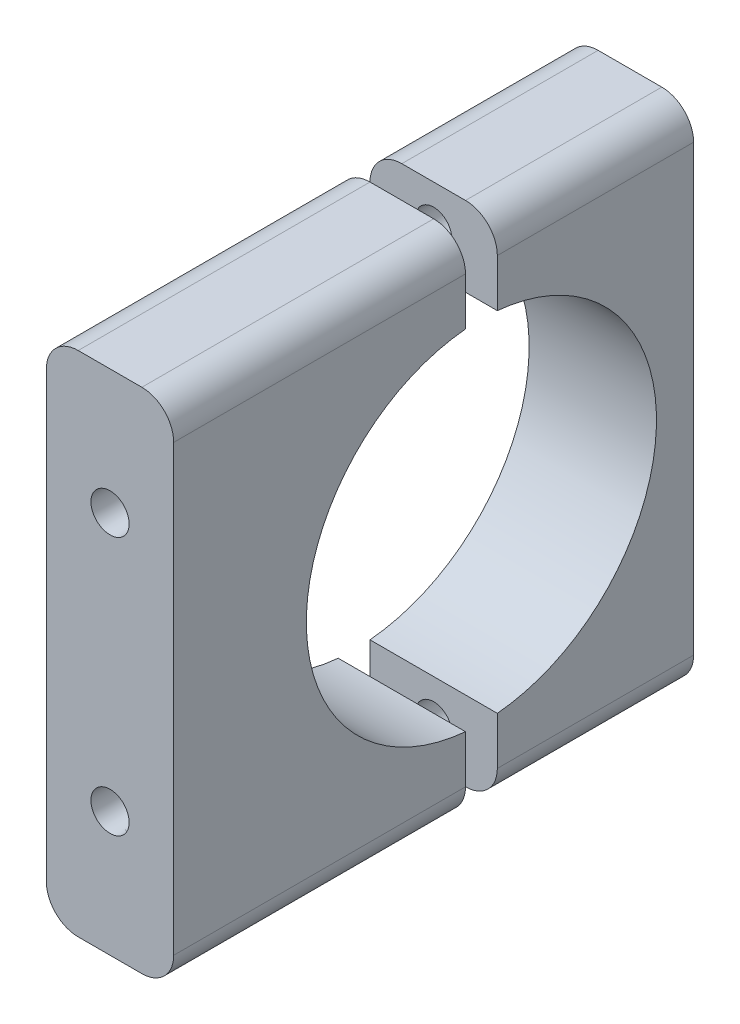
SolidWorks part; units mm, degrees
material "ABS"
ref_plane "Front Plane" through (0, 0, 0) normal (0, 0, 1) x (1, 0, 0)
ref_plane "Top Plane" through (0, 0, 0) normal (0, 1, 0) x (1, 0, 0)
ref_plane "Right Plane" through (0, 0, 0) normal (1, 0, 0) x (0, 0, -1)
sketch "Sketch1" plane through (0, 0, 0) normal (1, 0, 0) x (0, 0, -1)
  line L0 (-1.5, 16.4317) -> (-1.5, 23.9317) construction
  line L1 (-1.5, 23.9317) -> (-29, 23.9317) construction
  line L2 (-29, 23.9317) -> (-29, -23.9317) construction
  line L3 (-29, -23.9317) -> (-1.5, -23.9317) construction
  line L4 (-1.5, -23.9317) -> (-1.5, -16.4317) construction
  line L5 (1.5, 23.9317) -> (1.5, 16.4317) construction
  line L6 (20, 23.9317) -> (1.5, 23.9317) construction
  line L7 (20, -23.9317) -> (20, 23.9317) construction
  line L8 (1.5, -23.9317) -> (20, -23.9317) construction
  line L9 (1.5, -16.4317) -> (1.5, -23.9317) construction
  line L10 (-1.5, 16.4317) -> (-1.5, 23.9317)
  line L11 (-1.5, 23.9317) -> (-29, 23.9317)
  line L12 (-29, 23.9317) -> (-29, -23.9317)
  line L13 (-29, -23.9317) -> (-1.5, -23.9317)
  line L14 (-1.5, -23.9317) -> (-1.5, -16.4317)
  line L15 (1.5, 23.9317) -> (1.5, 16.4317)
  line L16 (20, 23.9317) -> (1.5, 23.9317)
  line L17 (20, -23.9317) -> (20, 23.9317)
  line L18 (1.5, -23.9317) -> (20, -23.9317)
  line L19 (1.5, -16.4317) -> (1.5, -23.9317)
  circle A1 centre (0, 0) radius 16.5
  circle A2 centre (0, 0) radius 16.5
  dimension "D1" = 0
extrude "Boss-Extrude1" add sketch "Sketch1" along normal blind 12 contours A2 L19 L18 L17 L16 L15 | A2 L10 L11 L12 L13 L14
sketch "Sketch2" plane through (0, 0, 0) normal (0, 0, 1) x (1, 0, 0)
  line L0 (0, 20.1817) -> (12, 20.1817) construction
  line L1 (6.6, 0) -> (-6.6, 0) construction
  line L2 (0, -20.1817) -> (12, -20.1817) construction
  line L3 (6, 20.1817) -> (6, 12.1817)
  line L4 (0, 23.9317) -> (0, 16.4317)
  line L5 (12, 23.9317) -> (0, 23.9317)
  line L6 (12, 16.4317) -> (12, 23.9317)
  line L7 (0, 16.4317) -> (12, 16.4317)
  line L8 (0, 23.9317) -> (0, 16.4317)
  line L9 (12, 23.9317) -> (0, 23.9317)
  line L10 (12, 16.4317) -> (12, 23.9317)
  line L11 (0, 16.4317) -> (12, 16.4317)
  line L12 (6, -20.1817) -> (6, -12.1817)
  circle A0 centre (6, 20.1817) radius 1.4073
  circle A1 centre (6, -20.1817) radius 1.4073
  dimension "D2" = 8
  dimension "D1" = 0
fillet "Fillet1" radius 3 4 edges at (0, -23.9317, -10.75) (12, -23.9317, -10.75) (0, 23.9317, -10.75) (12, 23.9317, -10.75)
fillet "Fillet2" radius 3 4 edges at (12, 23.9317, 15.25) (12, -23.9317, 15.25) (0, -23.9317, 15.25) (0, 23.9317, 15.25)
hole_wizard "CBORE for M3 SHCS1" positions "Sketch5" profile "Sketch6" counterbore size "M3" standard "ANSI Metric" end condition through all
sketch "Sketch5" plane through (0, 0, -20) normal (0, 0, -1) x (-1, 0, 0)
  point P0 (-6, 20.1817)
  point P3 (-6, -20.1817)
sketch "Sketch6" plane through (6, 20.1817, -20) normal (1, 0, 0) x (0, 1, 0)
  line L0 (0, 0) -> (0, 49)
  line L1 (0, 49) -> (1.7, 49)
  line L3 (1.7, 49) -> (1.7, 10)
  line L4 (3.25, 10) -> (1.7, 10)
  line L5 (3.25, 10) -> (3.25, 0.025)
  line L6 (3.25, 0.025) -> (3.275, 0)
  line L7 (3.275, 0) -> (0, 0)
  line L8 (-3.25, 0.025) -> (-3.275, 0) construction
  line L11 (0, -6.35) -> (0, 107.95) construction
  dimension "Thru Hole Dia." = 3.4
  dimension "Thru Hole Depth" = 49
  dimension "C'Bore Dia." = 6.5
  dimension "C'Bore Depth" = 10
  dimension "Near C'Sink Dia." = 6.55
  dimension "Near C'Sink Angle" = 90
hole_wizard "Hole1" positions "Sketch7" profile "Sketch8" legacy
sketch "Sketch7" plane through (0, 0, 1.5) normal (0, 0, -1) x (-1, 0, 0)
  point P0 (-6, 20.1817)
  point P3 (-6, -20.1817)
sketch "Sketch8" plane through (6, 20.1817, 1.5) normal (1, 0, 0) x (0, 1, 0)
  line L0 (0, 0) -> (0, 6)
  line L1 (0, 6) -> (1.8, 6)
  line L2 (1.8, 6) -> (1.8, 0)
  line L3 (1.8, 0) -> (0, 0)
  line L4 (0, 110) -> (0, -10) construction
  dimension "Diameter" = 3.6
  dimension "Depth" = 6
hole_wizard "Hole2" positions "Sketch9" profile "Sketch10" legacy
sketch "Sketch9" plane through (0, 0, -20) normal (0, 0, -1) x (-1, 0, 0)
  point P0 (-6, 12.1817)
  point P3 (-6, -12.1817)
sketch "Sketch10" plane through (6, 12.1817, -20) normal (1, 0, 0) x (0, 1, 0)
  line L0 (0, 0) -> (0, 4)
  line L1 (0, 4) -> (1.8, 4)
  line L2 (1.8, 4) -> (1.8, 0)
  line L3 (1.8, 0) -> (0, 0)
  line L4 (0, 110) -> (0, -10) construction
  dimension "Diameter" = 3.6
  dimension "Depth" = 4
hole_wizard "Hole3" positions "Sketch13" profile "Sketch14" legacy
sketch "Sketch13" plane through (0, 0, 29) normal (0, 0, 1) x (1, 0, 0)
  point P0 (6, 12.1817)
  point P3 (6, -12.1817)
sketch "Sketch14" plane through (6, 12.1817, 29) normal (1, 0, 0) x (0, -1, 0)
  line L0 (0, 0) -> (0, 6)
  line L1 (0, 6) -> (1.8, 6)
  line L2 (1.8, 6) -> (1.8, 0)
  line L3 (1.8, 0) -> (0, 0)
  line L4 (0, 110) -> (0, -10) construction
  dimension "Diameter" = 3.6
  dimension "Depth" = 6
draft "Draft1" type of draft neutral plane draft angle 2 faces to draft 2 face at (4.2, -12.1817, -16) face at (4.2, 12.1817, -16) neutral plane through (12, 0, -20) neutral plane normal (0, 0, -1) parameters "D1"=2
draft "Draft2" type of draft neutral plane draft angle 2 faces to draft 2 face at (6, -18.3817, 7.5) face at (6, 21.9817, 7.5) neutral plane through (12, 0, 1.5) neutral plane normal (0, 0, -1) parameters "D1"=2
draft "Draft3" type of draft neutral plane draft angle 2 faces to draft 2 face at (7.8, -12.1817, 23) face at (7.8, 12.1817, 23) neutral plane through (12, 0, 29) neutral plane normal (0, 0, 1) parameters "D1"=2
